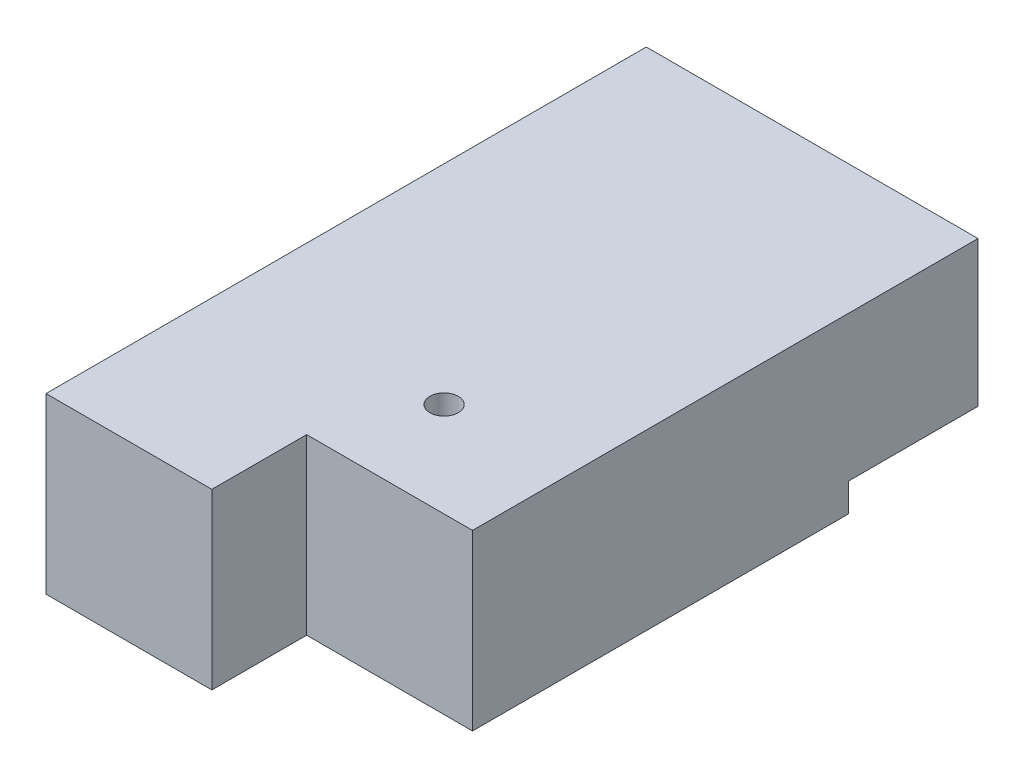
SolidWorks part; units mm, degrees
ref_plane "前视基准面" through (0, 0, 0) normal (0, 0, 1) x (1, 0, 0)
ref_plane "上视基准面" through (0, 0, 0) normal (0, 1, 0) x (1, 0, 0)
ref_plane "右视基准面" through (0, 0, 0) normal (1, 0, 0) x (0, 0, -1)
sketch "草图1" plane through (0, 0, 0) normal (0, 1, 0) x (1, 0, 0)
  line L1 (-10.5, 19) -> (10.5, 19)
  line L2 (-10.5, 19) -> (-10.5, -19)
  line L3 (-10.5, -19) -> (10.5, -19)
  line L4 (10.5, 19) -> (10.5, -19)
  line L5 (-10.5, 19) -> (10.5, -19) construction
  line L6 (-10.5, -19) -> (10.5, 19) construction
  point P0 (0, 0)
  dimension "D1" = 21
  dimension "D2" = 38
extrude "凸台-拉伸1" add sketch "草图1" along normal blind 11
sketch "草图2" plane through (0, 0, 0) normal (0, -1, 0) x (1, 0, 0)
  line L0 (10.5, 19) -> (10.5, -19) construction
  line L1 (-10.5, -19) -> (10.5, -19)
  line L2 (-10.5, -19) -> (-10.5, -10.8)
  line L3 (-10.5, -10.8) -> (10.5, -10.8)
  line L4 (10.5, -19) -> (10.5, -10.8)
  dimension "D1" = 8.2
extrude "切除-拉伸1" cut sketch "草图2" against normal blind 1.8
sketch "草图3" plane through (0, 0, 19) normal (0, 0, 1) x (1, 0, 0)
  line L0 (-10.5, 11) -> (10.5, 11) construction
  line L1 (10.5, 0) -> (0, 0)
  line L2 (10.5, 0) -> (10.5, 11)
  line L3 (10.5, 11) -> (0, 11)
  line L4 (0, 0) -> (0, 11)
extrude "切除-拉伸2" cut sketch "草图3" against normal blind 6
sketch "草图5" plane through (0, 11, 0) normal (0, 1, 0) x (1, 0, 0)
  line L0 (10.5, 19) -> (-10.5, 19) construction
  line L1 (10.5, -13) -> (10.5, 19) construction
  circle A0 centre (2.7, -7) radius 0.9
  dimension "D3" = 1.8
  dimension "D1" = 26
  dimension "D2" = 7.8
extrude "切除-拉伸3" cut sketch "草图5" against normal through all
